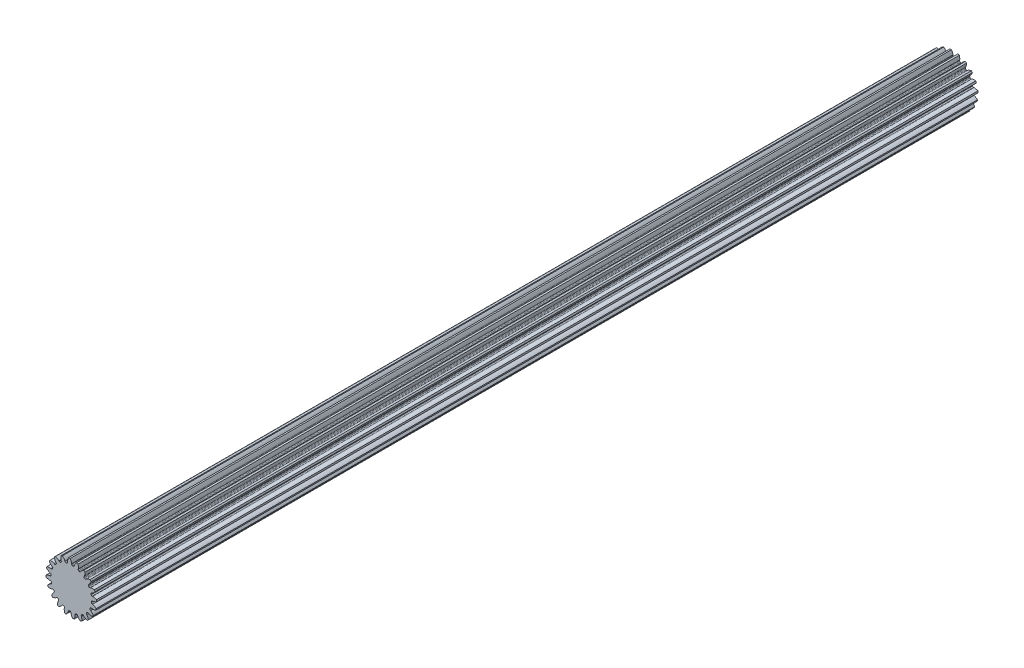
SolidWorks part; units mm, degrees
ref_plane "Front" through (0, 0, 0) normal (0, 0, 1) x (1, 0, 0)
ref_plane "Top" through (0, 0, 0) normal (0, 1, 0) x (1, 0, 0)
ref_plane "Right" through (0, 0, 0) normal (1, 0, 0) x (0, 0, -1)
sketch "Sketch1" plane through (0, 0, 0) normal (0, 0, 1) x (1, 0, 0)
  line L0 (-254, 0) -> (254, 0) construction
  circle A0 centre (0, 0) radius 8.763
  circle A1 centre (0, 0) radius 7.9375 construction
  circle A3 centre (0, 0) radius 7.0191 construction
  dimension "D1" = 0.9184
  dimension "OD" = 17.526
  dimension "D2" = 1.7439
  dimension "Root Dia" = 14.0383
  dimension "D3" = 0.8255
  dimension "Pitch Diameter" = 15.875
  dimension "Number of Teeth" = 508
extrude "Boss-Extrude1" add sketch "Sketch1" against normal blind 304.8
sketch "Sketch3" plane through (0, 0, 0) normal (0, 0, 1) x (1, 0, 0)
  line L0 (0, 0) -> (0, 8.763) construction
  line L1 (-2.5511, 7.009) -> (0, 7.9375)
  line L2 (-9.5921, 7.9375) -> (9.5921, 7.9375) construction
  line L3 (-9.0136, 4.6568) -> (9.0136, 11.2182) construction
  line L4 (-2.5511, 7.009) -> (0, 0) construction
  line L5 (-5.3715, 5.175) -> (0, 0) construction
  line L6 (-5.3715, 5.175) -> (-1.1335, 9.5739) construction
  line L7 (-1.7721, 7.2452) -> (0, 0) construction
  line L8 (-1.7721, 7.2452) -> (0.0739, 7.6967) construction
  arc A0 (-2.5511, 7.009) -> (-5.3715, 5.175) centre (0, 0) ccw
  circle A1 centre (0, 0) radius 7.9375 construction
  circle A2 centre (0, 0) radius 7.4588 construction
  arc A3 (-2.5511, 7.009) -> (-1.7721, 7.2452) centre (0, 0) cw
  circle A4 centre (0, 0) radius 8.763 construction
  point P6 (0, 7.9375)
  dimension "D1" = 2.7148
  dimension "Pressure Angle" = 20
  dimension "D2" = 3.3935
  dimension "D3" = 6.1083
  dimension "D4" = 0.8144
  dimension "D5" = 1.9003
sketch "Sketch4" plane through (0, 0, 0) normal (0, 0, 1) x (1, 0, 0)
  line L0 (0, 0) -> (0.6209, 7.8886) construction
  line L1 (0.1297, 7.4577) -> (0.1297, 7.0179)
  line L2 (0, 7.9375) -> (1.2417, 7.8398) construction
  line L3 (1.0386, 7.3861) -> (0.9698, 6.9518)
  line L4 (0.1297, 7.0179) -> (0, 0) construction
  line L5 (0, 0) -> (0, 8.763) construction
  line L6 (-5.3715, 5.175) -> (-1.1335, 9.5739) construction
  line L7 (-5.3715, 5.175) -> (-1.1335, 9.5739) construction
  arc A0 (0.9698, 6.9518) -> (0.1297, 7.0179) centre (0, 0) ccw
  arc A1 (0, 7.9375) -> (1.2417, 7.8398) centre (0, 0) cw construction
  circle A2 centre (0, 0) radius 7.9375 construction
  circle A3 centre (0, 0) radius 7.4588 construction
  circle A4 centre (0, 0) radius 7.0191 construction
  arc A5 (2.6173, 9.2787) -> (-1.1335, 9.5739) centre (0, 0) ccw
  spline S0 degree 2 poles (-1.1335, 9.5739) (-0.1134, 8.6803) (0.1297, 7.4577) knots 0 0 0 1 1 1
  spline S1 degree 2 poles (2.6173, 9.2787) (1.4699, 8.5557) (1.0386, 7.3861) knots 0 0 0 1 1 1
  dimension "D1" = 1.2468
extrude "Cut-Extrude1" cut sketch "Sketch4" against normal through all
fillet "Fillet1" radius 0.3117 2 edges at (0.9698, 6.9518, -152.4) (0.1297, 7.0179, -152.4)
pattern_circular "CirPattern1" count 20 over 360 about axis through (0, 0, -304.8) along (0, 0, 1) of "Cut-Extrude1", "Fillet1"
sketch "Pitch Dia" plane through (0, 0, 0) normal (0, 0, 1) x (1, 0, 0)
  circle A0 centre (0, 0) radius 7.9375 construction
  circle A1 centre (0, 0) radius 7.9375
equation "\"D2@Sketch3\" = \"D1@Sketch3\"*1.25"
equation "\"D3@Sketch3\" = \"D1@Sketch3\"+\"D2@Sketch3\""
equation "\"D4@Sketch3\" = \"D1@Sketch3\"*.3"
equation "\"D5@Sketch3\" = \"D1@Sketch3\"-\"D4@Sketch3\""
equation "\"D1@Sketch4\" = 1.5708/(\"Number of Teeth@Sketch1\"/\"Pitch Diameter@Sketch1\")"
equation "\"D1@CirPattern1\" = \"Number of Teeth@Sketch1\""
equation "\"D1@Fillet1\" = \"D1@Sketch4\"*.25"
equation "\"D1@Sketch1\" = 1.157/(\"Number of Teeth@Sketch1\"/\"Pitch Diameter@Sketch1\")"
